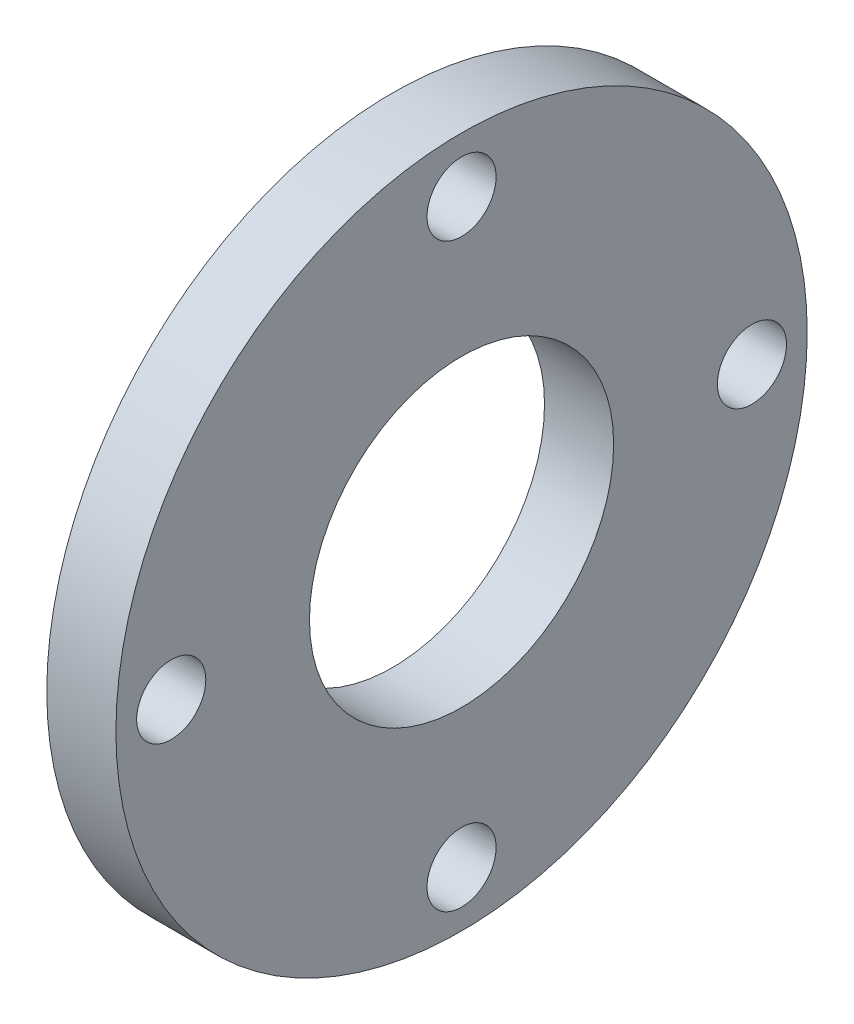
SolidWorks part; units mm, degrees
ref_plane "Alzado" through (0, 0, 0) normal (0, 0, 1) x (1, 0, 0)
ref_plane "Planta" through (0, 0, 0) normal (0, 1, 0) x (1, 0, 0)
ref_plane "Vista lateral" through (0, 0, 0) normal (1, 0, 0) x (0, 0, -1)
sketch "Croquis1" plane through (0, 0, 0) normal (1, 0, 0) x (0, 0, -1)
  circle A0 centre (0, 0) radius 25
  circle A1 centre (0, 0) radius 11
  dimension "D1" = 22
  dimension "D2" = 50
extrude "Saliente-Extruir1" add sketch "Croquis1" along normal blind 5
sketch "Croquis2" plane through (5, 0, 0) normal (1, 0, 0) x (0, 0, -1)
  circle A0 centre (0, 0) radius 21 construction
  circle A1 centre (0, 21) radius 2.5
  circle A2 centre (21, 0) radius 2.5
  circle A3 centre (0, -21) radius 2.5
  circle A4 centre (-21, 0) radius 2.5
  point P14 (0, 0)
  dimension "D1" = 42
  dimension "D3" = 5
  dimension "D2" = 4
extrude "Cortar-Extruir1" cut sketch "Croquis2" against normal blind 10
